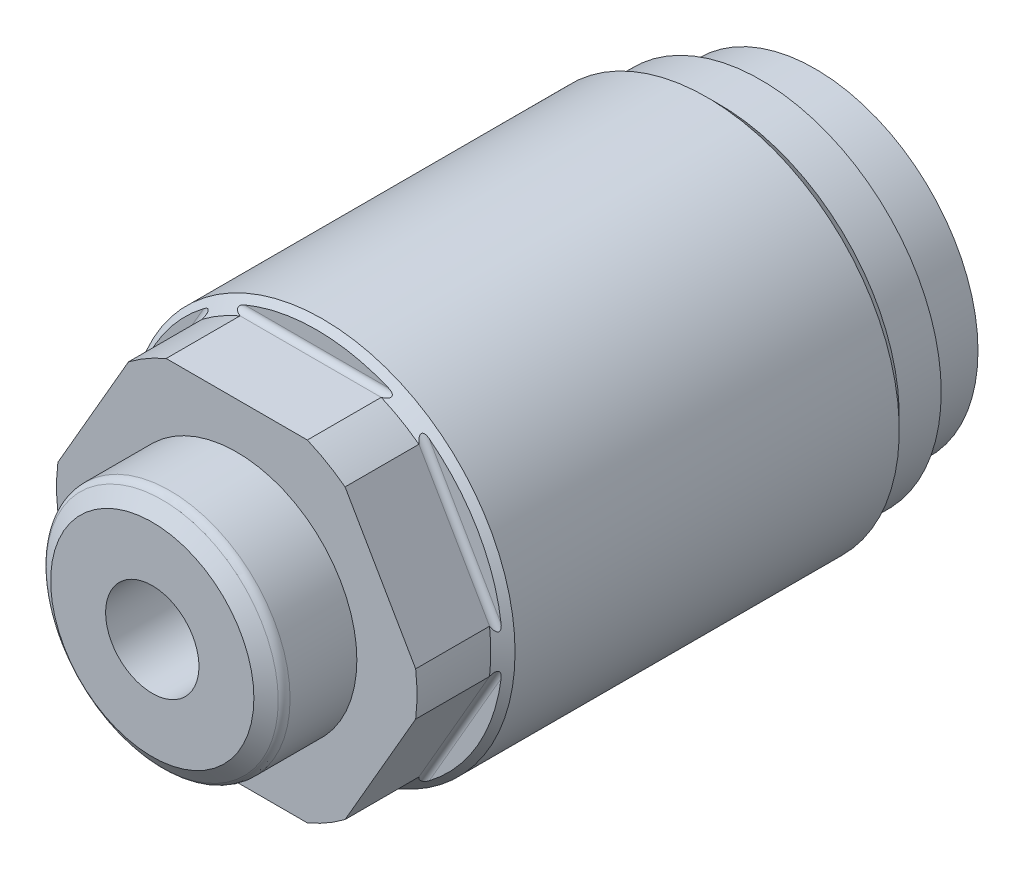
SolidWorks part; units mm, degrees
material "Alloy Steel"
ref_plane "Front Plane" through (0, 0, 0) normal (0, 0, 1) x (1, 0, 0)
ref_plane "Top Plane" through (0, 0, 0) normal (0, 1, 0) x (1, 0, 0)
ref_plane "Right Plane" through (0, 0, 0) normal (1, 0, 0) x (0, 0, -1)
ref_plane "Plane1" through (0, 0, 0) normal (0, 0, 1) x (1, 0, 0)
sketch "Sketch1" plane through (0, 0, 0) normal (0, 0, 1) x (1, 0, 0)
  circle A0 centre (0, 0) radius 16.5354
extrude "Extrude1" add sketch "Sketch1" along normal blind 49.7332
ref_plane "Plane2" through (0, 0, 0) normal (1, 0, 0) x (0, 0, 1)
sketch "Sketch2" plane through (0, 0, 0) normal (1, 0, 0) x (0, 0, 1)
  line L0 (42.8752, 16.5354) -> (42.8752, 14.7637)
  line L1 (43.3832, 14.2557) -> (49.7332, 14.2557)
  line L2 (42.5323, 0) -> (50.0761, 0) construction
  line L3 (49.7332, -16.5354) -> (49.7332, 16.5354) construction
  line L4 (42.8752, 16.5354) -> (49.7332, 16.5354)
  line L5 (49.7332, 16.5354) -> (49.7332, 14.2557)
  arc A0 (42.8752, 14.7637) -> (43.3832, 14.2557) centre (43.3832, 14.7637) ccw
  dimension "D2" = 0.508
  dimension "D1" = 28.5115
  dimension "D3" = 6.858
extrude "Cut-Extrude1" cut sketch "Sketch2" against normal mid plane 39.685
ref_plane "Plane12" through (0, 0, 0) normal (1, 0, 0) x (0, 0, -1)
sketch "Sketch10" plane through (0, 0, 0) normal (1, 0, 0) x (0, 0, -1)
  line L0 (-49.7332, 15.494) -> (-43.3832, 15.494)
  line L1 (-43.3832, 15.494) -> (-42.3418, 16.5354)
  line L2 (-42.3418, 16.5354) -> (-49.7332, 16.5354)
  line L3 (-49.7332, 16.5354) -> (-49.7332, 15.494)
  line L4 (-50.1028, 0) -> (-41.9722, 0) construction
  line L5 (0, 16.5354) -> (-49.7332, 16.5354) construction
  line L6 (-49.7332, 16.5354) -> (-49.7332, -14.2557) construction
  dimension "D1" = 30.988
  dimension "D2" = 45
  dimension "D3" = 6.35
revolve "Cut-Revolve1" cut sketch "Sketch10" angle 360 about L4
ref_plane "Plane13" through (0, 0, 0) normal (1, 0, 0) x (0, 0, 1)
sketch "Sketch11" plane through (0, 0, 0) normal (1, 0, 0) x (0, 0, 1)
  line L0 (0, 15.5067) -> (8.2804, 15.5067)
  line L1 (8.2804, 15.5067) -> (9.3091, 16.5354)
  line L2 (9.3091, 16.5354) -> (0, 16.5354)
  line L3 (0, 16.5354) -> (0, 15.5067)
  line L4 (-0.4655, 0) -> (9.7746, 0) construction
  line L5 (0, 16.5354) -> (0, -16.5354) construction
  line L6 (42.3418, 16.5354) -> (0, 16.5354) construction
  dimension "D1" = 31.0134
  dimension "D2" = 8.2804
  dimension "D3" = 45
revolve "Cut-Revolve2" cut sketch "Sketch11" angle 360 about L4
ref_plane "Plane14" through (0, 0, 0) normal (1, 0, 0) x (0, 0, -1)
sketch "Sketch12" plane through (0, 0, 0) normal (1, 0, 0) x (0, 0, -1)
  line L0 (-4.6736, 15.5067) -> (0, 15.5067)
  line L1 (0, 15.5067) -> (0, 13.9954)
  line L2 (0, 13.9954) -> (-4.6736, 13.9954)
  line L3 (-4.6736, 13.9954) -> (-4.6736, 15.5067)
  line L4 (-4.9073, 0) -> (0.2337, 0) construction
  line L5 (0, 15.5067) -> (-8.2804, 15.5067) construction
  line L6 (0, -15.5067) -> (0, 15.5067) construction
  dimension "D1" = 27.9908
  dimension "D2" = 4.6736
revolve "Cut-Revolve3" cut sketch "Sketch12" angle 360 about L4
ref_plane "Plane15" through (0, 0, 0) normal (1, 0, 0) x (0, 0, -1)
sketch "Sketch13" plane through (0, 0, 0) normal (1, 0, 0) x (0, 0, -1)
  line L0 (-49.7332, 0) -> (-56.9976, 0)
  line L1 (-56.9976, 0) -> (-56.9976, 10.3251)
  line L2 (-56.9976, 10.3251) -> (-49.7332, 10.3251)
  line L3 (-49.7332, 10.3251) -> (-49.7332, 0)
  line L4 (-57.3608, 0) -> (-34.0678, 0) construction
  line L5 (-49.7332, 15.494) -> (-49.7332, -14.2557) construction
  dimension "D1" = 7.2644
  dimension "D2" = 20.6502
revolve "Revolve1" add sketch "Sketch13" angle 360 about L4
ref_plane "Plane16" through (-4.0132, 0, 56.9976) normal (0, 1, 0) x (-1, 0, 0)
sketch "S2D0011" plane through (-4.0132, 0, 56.9976) normal (0, 1, 0) x (-1, 0, 0)
  line L0 (0, 0) -> (0, -9.652)
  line L1 (0, -9.652) -> (-4.0132, -9.652)
  line L2 (0, 0) -> (-4.0132, 0)
  line L3 (-4.0132, 0) -> (-4.0132, -9.652)
  line L4 (-4.0132, -24.9949) -> (-4.0132, 0.4826) construction
  line L5 (6.3119, 0) -> (-14.3383, 0) construction
  dimension "D1" = 8.0264
  dimension "D2" = 9.652
revolve "Cut-Revolve4" cut sketch "S2D0011" angle 360 about L4
ref_plane "Plane17" through (0, 0, 0) normal (1, 0, 0) x (0, 0, -1)
sketch "Sketch15" plane through (0, 0, 0) normal (1, 0, 0) x (0, 0, -1)
  line L0 (-56.9976, 8.7376) -> (-56.1421, 9.9746)
  line L1 (-57.0738, 0) -> (-47.2378, 0) construction
  line L2 (-49.7332, 10.3251) -> (-56.9976, 10.3251) construction
  line L3 (-56.9976, 8.7376) -> (-56.9976, 10.3251)
  line L4 (-56.9976, 10.3251) -> (-55.4736, 10.3251)
  arc A0 (-55.4736, 10.3251) -> (-56.1421, 9.9746) centre (-55.4736, 9.5123) ccw
  dimension "D3" = 0.8128
  dimension "D1" = 17.4752
  dimension "D2" = 1.524
revolve "Cut-Revolve5" cut sketch "Sketch15" angle 360 about L1
pattern_circular "CirPattern2" count 6 over 360 about axis through (0, 0, 0) along (0, 0, 1) of "Cut-Extrude1"
